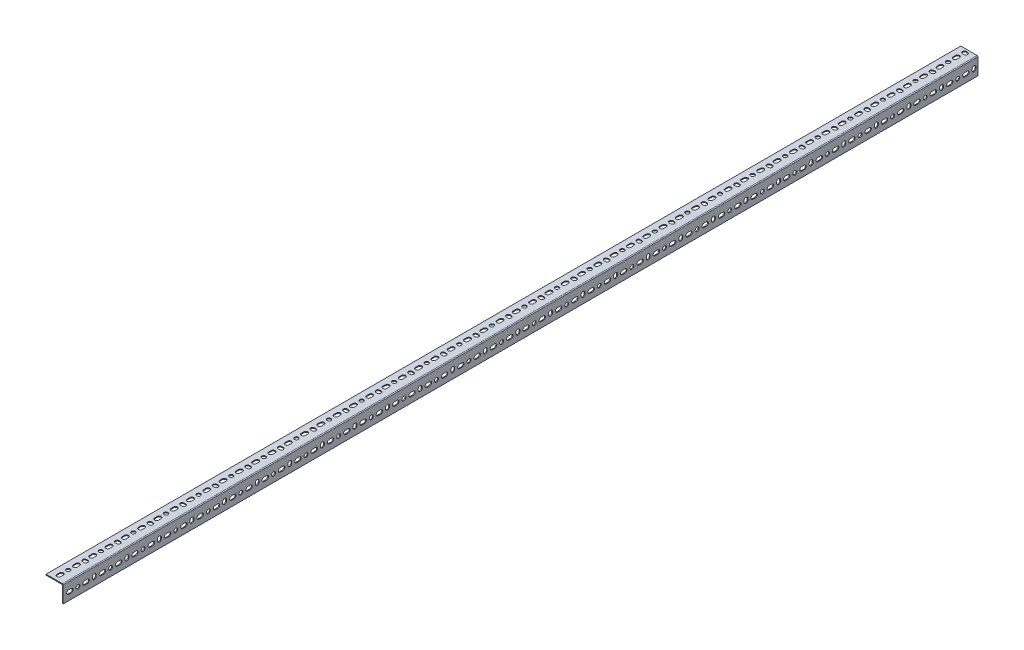
SolidWorks part; units mm, degrees
material "Black Iron Steel"
ref_plane "Front Plane" through (0, 0, 0) normal (0, 0, 1) x (1, 0, 0)
ref_plane "Top Plane" through (0, 0, 0) normal (0, 1, 0) x (1, 0, 0)
ref_plane "Right Plane" through (0, 0, 0) normal (1, 0, 0) x (0, 0, -1)
other "Length"
sketch "Sketch2" plane through (0, 0, 0) normal (0, 1, 0) x (1, 0, 0)
  line L0 (0, 0) -> (0, 2133.6)
  dimension "D1" = 2133.6
other "Structural Member1"
ref_plane "Plane1" through (0, 0, 0) normal (0, 0, -1) x (-1, 0, 0)
sketch "Sketch13" plane through (0, 0, 0) normal (0, 0, -1) x (-1, 0, 0)
  line L0 (40.1, 0) -> (2, 0)
  line L1 (0, -2) -> (0, -40.1)
  line L2 (39.1, -2) -> (4, -2)
  line L3 (2, -4) -> (2, -39.1)
  line L4 (40.1, 0) -> (40.1, -1)
  line L5 (0, -40.1) -> (1, -40.1)
  arc A0 (40.1, -1) -> (39.1, -2) centre (39.1, -1) cw
  arc A1 (1, -40.1) -> (2, -39.1) centre (1, -39.1) ccw
  arc A2 (4, -2) -> (2, -4) centre (4, -4) ccw
  arc A3 (2, 0) -> (0, -2) centre (2, -2) ccw
  point P2 (21.05, 0)
  point P13 (0, -21.05)
  point P17 (0, 0)
  point P18 (0, 0)
  dimension "r1" = 1
  dimension "r" = 2
  dimension "D1" = 2
  dimension "b" = 40.1
  dimension "d" = 2
sketch "Sketch3" plane through (0, 0, 0) normal (0, 1, 0) x (1, 0, 0)
  line L0 (-22.6, 12.5) -> (-22.6, 18.5) construction
  line L1 (-27.1, 12.5) -> (-27.1, 18.5)
  line L2 (-18.1, 12.5) -> (-18.1, 18.5)
  line L3 (-40.1, 0) -> (-2, 0) construction
  line L4 (-40.1, 2133.6) -> (-40.1, 0) construction
  arc A0 (-27.1, 12.5) -> (-18.1, 12.5) centre (-22.6, 12.5) ccw
  arc A1 (-18.1, 18.5) -> (-27.1, 18.5) centre (-22.6, 18.5) ccw
  point P2 (-22.6, 15.5)
  dimension "D1" = 15
  dimension "D3" = 8
  dimension "D2" = 9
  dimension "D4" = 13
extrude "Slot" cut sketch "Sketch3" against normal through all
sketch "Sketch4" plane through (0, 0, 0) normal (0, 1, 0) x (1, 0, 0)
  line L0 (-22.6, 34.5) -> (-22.6, 15.5) construction
  line L1 (-22.6, 12.5) -> (-22.6, 18.5) construction
  circle A0 centre (-22.6, 34.5) radius 4.5
  arc A1 (-18.1, 18.5) -> (-27.1, 18.5) centre (-22.6, 18.5) ccw construction
  dimension "D1" = 7
  dimension "D2" = 9
extrude "Hole" cut sketch "Sketch4" against normal through all
sketch "Sketch14" plane through (0, 0, 0) normal (0, 1, 0) x (1, 0, 0)
  line L0 (-19.6, 72.5) -> (-22.6, 72.5) construction
  line L1 (-19.6, 68) -> (-22.6, 68)
  line L2 (-19.6, 77) -> (-22.6, 77)
  arc A0 (-19.6, 68) -> (-19.6, 77) centre (-19.6, 72.5) ccw
  arc A1 (-22.6, 77) -> (-22.6, 68) centre (-22.6, 72.5) ccw
  point P2 (-21.1, 72.5)
  dimension "D2" = 12
  dimension "D1" = 9
  dimension "D3" = 38
extrude "Vert Slot" cut sketch "Sketch14" against normal through all
pattern_linear "Slot Pattern" count 56 spacing 38 along (0, 0, -1) of "Slot"
pattern_linear "Hole Pattern" count 28 spacing 76 along (0, 0, -1) of "Hole"
pattern_linear "LPattern1" count 28 spacing 76 along (0, 0, -1) of "Vert Slot"
pattern_circular "Other side cuts" count 2 every 90 about axis through (-4, -4, 0) along (0, 0, 1) of "Slot", "Hole", "Vert Slot", "Slot Pattern", "Hole Pattern", "LPattern1"
equation "\"D1@Sketch13\" = \"r@Sketch13\""
